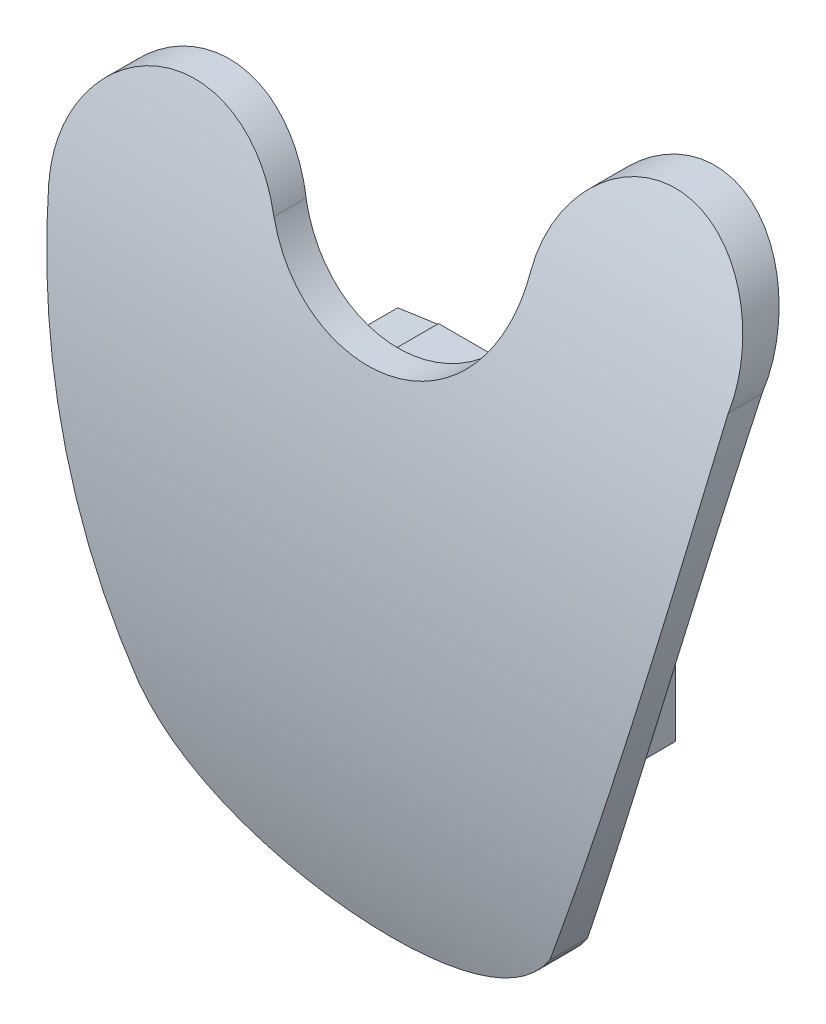
SolidWorks part; units mm, degrees
ref_plane "Front Plane" through (0, 0, 0) normal (0, 0, 1) x (1, 0, 0)
ref_plane "Top Plane" through (0, 0, 0) normal (0, 1, 0) x (1, 0, 0)
ref_plane "Right Plane" through (0, 0, 0) normal (1, 0, 0) x (0, 0, -1)
sketch "Sketch2" plane through (0, 0, 0) normal (0, 0, 1) x (1, 0, 0)
  line L0 (-53.9085, 0) -> (53.9085, 0) construction
  line L1 (0, -51.9917) -> (0, 51.9917) construction
  circle A2 centre (0, 0) radius 8
  circle A4 centre (-14.5, 0) radius 6.5
  circle A5 centre (14.5, 0) radius 6.5
  circle A6 centre (0, -45) radius 5
  spline S0 degree 2 poles (-20.9029, -1.1191) (-19.287, -26.3677) (-3.9318, -48.0888) knots 0 0 0 1 1 1
  spline S1 degree 2 poles (20.9029, -1.1191) (19.287, -26.3677) (3.9318, -48.0888) knots 0 0 0 1 1 1
  point P4 (0, 0)
  point P10 (0, 0)
  dimension "D1" = 16
  dimension "D2" = 13
  dimension "D3" = 10
  dimension "D4" = 45
extrude "Boss-Extrude1" add sketch "Sketch2" along normal blind 10
sketch "Sketch3" plane through (0, 0, 0) normal (1, 0, 0) x (0, 0, -1)
  line L0 (0, 6.5) -> (-10, 6.5) construction
  line L1 (-10, -50) -> (0, -50) construction
  line L2 (-2.5, 6.5) -> (0, 6.5)
  line L3 (-13.8007, 11.8169) -> (12.5486, 11.8169)
  line L4 (-13.8007, 11.8169) -> (-13.8007, -57.027)
  line L5 (-13.8007, -57.027) -> (12.5486, -57.027)
  line L6 (12.5486, 11.8169) -> (12.5486, -57.027)
  line L7 (-2.5, -50) -> (0, -50)
  spline S0 degree 2 poles (0, 6.5) (-14.4085, -21.082) (0, -50) knots 0 0 0 1 1 1
  spline S1 degree 3 poles (-2.5, 6.5) (-10.7335, -10.9766) (-12.0539, -32.6497) (-2.5, -50) knots 0 0 0 0 1 1 1 1
  dimension "D1" = 2.5
  dimension "D2" = 2.5
extrude "Cut-Extrude1" cut sketch "Sketch3" against normal through all both and the other way through all
sketch "Sketch6" plane through (0, 0, 0) normal (0, 0, 1) x (1, 0, 0)
  line L0 (-9.5574, -39.2004) -> (-14.8262, -49.9238)
  line L1 (-14.8262, -49.9238) -> (21.9396, -53.6004)
  line L2 (21.9396, -53.6004) -> (9.5574, -39.2004)
  parabola Q0 (-20.9029, -1.1191) -> (-3.9318, -48.0888) focus (23.8791, -6.6776) apex (-18.3118, -17.5099) construction
  parabola Q1 (20.9029, -1.1191) -> (3.9318, -48.0888) focus (-23.8791, -6.6776) apex (18.3118, -17.5099) construction
  parabola Q2 (-20.9029, -1.1191) -> (-3.9318, -48.0888) focus (23.8791, -6.6776) apex (-18.3118, -17.5099) construction
  parabola Q3 (20.9029, -1.1191) -> (3.9318, -48.0888) focus (-23.8791, -6.6776) apex (18.3118, -17.5099) construction
  spline S0 degree 3 poles (-9.5574, -39.2004) (-5.9429, -46.0063) (5.8575, -45.9212) (9.5574, -39.2004) knots 0 0 0 0 1 1 1 1
extrude "Cut-Extrude2" cut sketch "Sketch6" against normal through all both and the other way through all
sketch "Sketch8" plane through (0, 0, 0) normal (0, 0, 1) x (1, 0, 0)
  line L0 (-13.816, -30.617) -> (-11.7641, -45.7248)
  line L1 (-11.7641, -45.7248) -> (9.7245, -47.8372)
  line L2 (9.7245, -47.8372) -> (13.816, -30.617)
  parabola Q0 (-20.9029, -1.1191) -> (-9.3447, -39.5774) focus (23.8791, -6.6776) apex (-18.3118, -17.5099) construction
  parabola Q1 (20.9029, -1.1191) -> (9.4819, -39.3347) focus (-23.8791, -6.6776) apex (18.3118, -17.5099) construction
  parabola Q2 (-20.9029, -1.1191) -> (-9.3447, -39.5774) focus (23.8791, -6.6776) apex (-18.3118, -17.5099) construction
  spline S0 degree 3 poles (-13.816, -30.617) (-9.7781, -41.1606) (10.7723, -42.7036) (13.816, -30.617) knots 0 0 0 0 1 1 1 1
extrude "Cut-Extrude4" cut sketch "Sketch8" along normal blind 10
sketch "Sketch9" plane through (0, 0, 0) normal (0, 0, 1) x (1, 0, 0)
  line L0 (-20.1783, -8.0292) -> (-28.0859, 3.222)
  line L1 (-28.0859, 3.222) -> (-10.0442, 8.3657)
  line L2 (-10.0442, 8.3657) -> (-4.8227, -1.2981)
  line L3 (-4.8227, -1.2981) -> (-7.0096, -3.8599)
  circle A3 centre (-13.2498, -7.0316) radius 7
  arc A4 (-8, 0) -> (8, 0) centre (0, 0) ccw construction
  dimension "D1" = 14
extrude "Cut-Extrude5" cut sketch "Sketch9" against normal through all both and the other way through all contours A3 L3 L2 L1 L0
sketch "Sketch10" plane through (0, 0, 0) normal (0, 0, 1) x (1, 0, 0)
  line L0 (-7.6159, -15.9307) -> (-5.4681, -30.9307)
  line L1 (-5.4681, -30.9307) -> (-8.4378, -31.3559)
  line L2 (-8.4378, -31.3559) -> (-10.5856, -16.3559)
  line L3 (-10.5856, -16.3559) -> (-7.6159, -15.9307)
  point P4 (0, 0)
  point P5 (0, 0)
  point P6 (-9.5626, -19.9195)
  point P7 (-10.7655, -16.1288)
  point P8 (-9.9365, -31.0089)
  dimension "D1" = 3
  dimension "D2" = 15
extrude "Boss-Extrude2" add sketch "Sketch10" along normal blind 13 from offset 5 offset against normal yes
sketch "Sketch11" plane through (0, 0, 0) normal (1, 0, 0) x (0, 0, -1)
  line L0 (-6.3197, -31.3559) -> (5, -31.3559) construction
  line L1 (5, -15.9307) -> (2, -15.9307)
  line L2 (5, -15.9307) -> (5, -31.3559)
  line L3 (5, -31.3559) -> (2, -31.3559)
  line L4 (2, -15.9307) -> (2, -31.3559)
  dimension "D1" = 3
extrude "Boss-Extrude4" add sketch "Sketch11" against normal blind 15 from offset 7
